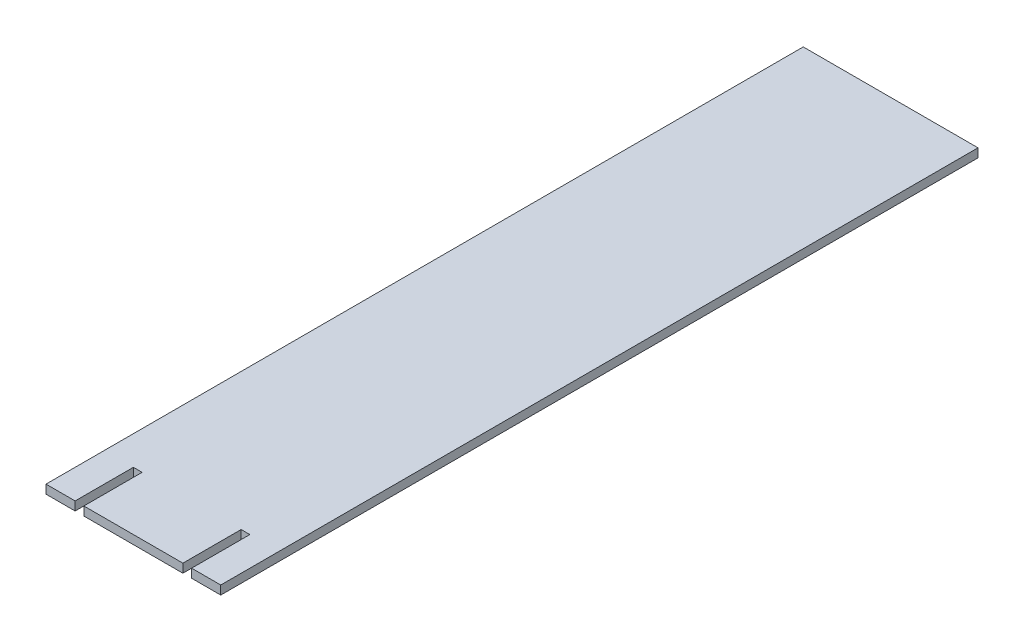
SolidWorks part; units mm, degrees
ref_plane "Front Plane" through (0, 0, 0) normal (0, 0, 1) x (1, 0, 0)
ref_plane "Top Plane" through (0, 0, 0) normal (0, 1, 0) x (1, 0, 0)
ref_plane "Right Plane" through (0, 0, 0) normal (1, 0, 0) x (0, 0, -1)
sketch "Sketch1" plane through (0, 0, 0) normal (0, 1, 0) x (1, 0, 0)
  line L0 (0, 0) -> (10, 0)
  line L2 (0, 0) -> (0, 260)
  line L3 (0, 260) -> (60, 260)
  line L4 (60, 0) -> (60, 260)
  line L5 (13, 0) -> (47, 0)
  line L7 (10, 0) -> (10, 20)
  line L8 (10, 20) -> (13, 20)
  line L9 (13, 0) -> (13, 20)
  line L10 (50, 0) -> (60, 0)
  line L12 (47, 0) -> (47, 20)
  line L13 (47, 20) -> (50, 20)
  line L14 (50, 0) -> (50, 20)
extrude "Boss-Extrude1" add sketch "Sketch1" along normal blind 3
